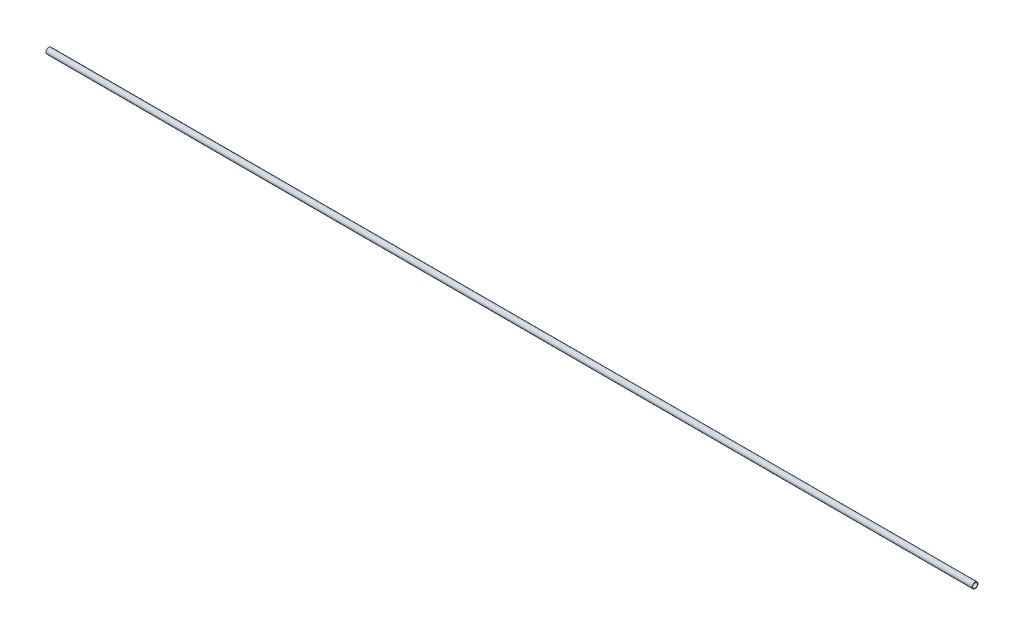
SolidWorks part; units mm, degrees
ref_plane "Front Plane" through (0, 0, 0) normal (0, 0, 1) x (1, 0, 0)
ref_plane "Top Plane" through (0, 0, 0) normal (0, 1, 0) x (1, 0, 0)
ref_plane "Right Plane" through (0, 0, 0) normal (1, 0, 0) x (0, 0, -1)
sketch "Sketch1" plane through (0, 0, 0) normal (1, 0, 0) x (0, 0, -1)
  circle A0 centre (0, 0) radius 3.81
  dimension "D1" = 7.62
extrude "Boss-Extrude1" add sketch "Sketch1" along normal blind 1219.2
sketch "Sketch2" plane through (0, 0, 0) normal (-1, 0, 0) x (0, 0, 1)
  circle A0 centre (0, 0) radius 3.175
  dimension "D1" = 6.35
extrude "Cut-Extrude1" cut sketch "Sketch2" against normal through all
